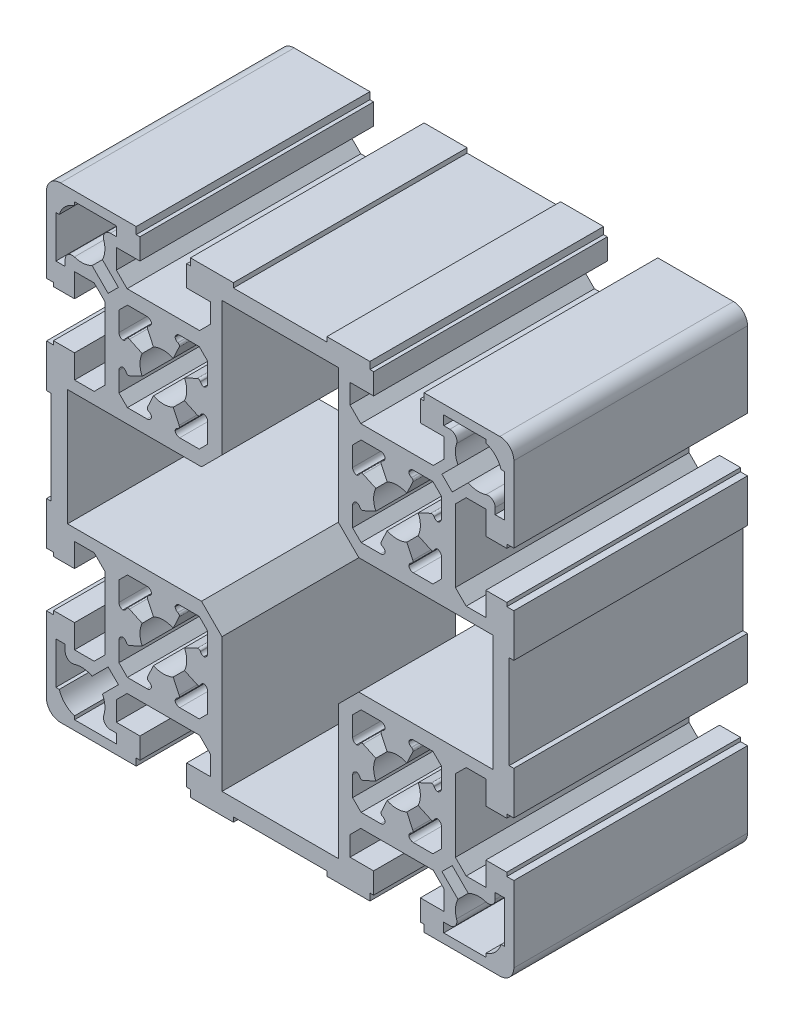
SolidWorks part; units mm, degrees
material "АД31Т ГОСТ 4784-97"
ref_plane "Front Plane" through (0, 0, 0) normal (0, 0, 1) x (1, 0, 0)
ref_plane "Top Plane" through (0, 0, 0) normal (0, 1, 0) x (1, 0, 0)
ref_plane "Right Plane" through (0, 0, 0) normal (1, 0, 0) x (0, 0, -1)
sketch "Sketch1" plane through (0, 0, 0) normal (0, 0, 1) x (1, 0, 0)
  line L0 (-15.5014, -32.6803) -> (-17.3205, -34.4994)
  line L1 (-12.45, -16.8336) -> (-16.8336, -12.45)
  line L2 (-17.25, -37.5) -> (-14.95, -39.8)
  line L3 (-14.95, -44) -> (-20, -44)
  line L4 (-19.2, -50) -> (-10, -50)
  line L5 (-35.05, -44) -> (-35.05, -39.8)
  line L6 (-50, -30.8) -> (-50, -47)
  line L7 (-48, -44) -> (-48, -35)
  line L8 (-47, -50) -> (-30.8, -50)
  line L9 (-35, -48) -> (-44, -48)
  line L10 (-44, -48) -> (-44, -47.2697)
  line L11 (-47.2697, -44) -> (-48, -44)
  line L12 (-20, -44) -> (-20, -48.5)
  line L13 (-30, -48.5) -> (-30, -44)
  line L14 (-35, -46) -> (-35, -48)
  line L15 (-30.8, -50) -> (-30.8, -48.5)
  line L16 (-30.8, -48.5) -> (-30, -48.5)
  line L17 (-20, -48.5) -> (-19.2, -48.5)
  line L18 (-19.2, -48.5) -> (-19.2, -50)
  line L19 (-30, -44) -> (-35.05, -44)
  line L20 (-36.3153, -46) -> (-35, -46)
  line L21 (-22.8883, -20.4679) -> (-21.6205, -17.7489)
  line L22 (-28.3809, -17.7495) -> (-27.1136, -20.4674)
  line L23 (-34.5, -21.5) -> (-34.5, -17.3191)
  line L24 (-44, -20) -> (-44, -14.95)
  line L25 (-50, -10) -> (-50, -19.2)
  line L26 (-37.5, -17.25) -> (-37.5, -32.75)
  line L27 (-21.6205, -32.2499) -> (-22.8883, -29.531)
  line L28 (-27.1145, -29.531) -> (-28.3824, -32.2499)
  line L29 (-34.5014, -32.6803) -> (-34.5014, -28.4994)
  line L30 (-37.5, -32.75) -> (-39.8, -35.05)
  line L31 (-40.2429, -38.0385) -> (-36.814, -34.6096)
  line L32 (-34.6096, -36.814) -> (-38.0385, -40.2429)
  line L33 (-46, -35) -> (-46, -36.3153)
  line L34 (-44, -30) -> (-48.5, -30)
  line L35 (-48.5, -30) -> (-48.5, -30.8)
  line L36 (-48.5, -30.8) -> (-50, -30.8)
  line L37 (-39.8, -35.05) -> (-44, -35.05)
  line L38 (-44, -35.05) -> (-44, -30)
  line L39 (-48, -35) -> (-46, -35)
  line L40 (-36.814, -34.6096) -> (-34.6096, -36.814)
  line L41 (-32.75, -37.5) -> (-17.25, -37.5)
  line L42 (-35.05, -39.8) -> (-32.75, -37.5)
  line L43 (-28.1405, -32.9143) -> (-28.0788, -32.9431)
  line L44 (-28.5014, -34.4994) -> (-32.6823, -34.4994)
  line L45 (-32.6823, -34.4994) -> (-34.5014, -32.6803)
  line L46 (-17.3205, -34.4994) -> (-21.5014, -34.4994)
  line L47 (-21.924, -32.9431) -> (-21.8623, -32.9143)
  line L48 (-48.5, -20) -> (-44, -20)
  line L49 (-50, -19.2) -> (-48.5, -19.2)
  line L50 (-48.5, -19.2) -> (-48.5, -20)
  line L51 (-32.9451, -28.0768) -> (-32.9164, -28.1385)
  line L52 (-32.2519, -28.3804) -> (-29.533, -27.1125)
  line L53 (-20.4699, -27.1125) -> (-17.751, -28.3804)
  line L54 (-17.0865, -28.1385) -> (-17.0577, -28.0768)
  line L55 (-29.533, -22.8863) -> (-32.2519, -21.6185)
  line L56 (-32.9164, -21.8603) -> (-32.9437, -21.9226)
  line L57 (-17.0577, -21.922) -> (-17.0865, -21.8603)
  line L58 (-17.751, -21.6185) -> (-20.4699, -22.8863)
  line L59 (-39.8, -14.95) -> (-37.5, -17.25)
  line L60 (-16.8336, -12.45) -> (-45.5, -12.45)
  line L61 (-44, -14.95) -> (-39.8, -14.95)
  line L62 (-49, -10) -> (-50, -10)
  line L63 (-28.0774, -17.0563) -> (-28.1391, -17.0851)
  line L64 (-34.5, -17.3191) -> (-32.6809, -15.5)
  line L65 (-32.6809, -15.5) -> (-28.5, -15.5)
  line L66 (-21.8623, -17.0845) -> (-21.924, -17.0557)
  line L67 (-21.5014, -15.4994) -> (-17.3205, -15.4994)
  line L68 (50, -47) -> (50, -30.8)
  line L69 (48, -35) -> (48, -44)
  line L70 (35.05, -39.8) -> (35.05, -44)
  line L71 (14.95, -44) -> (14.95, -39.8)
  line L72 (12.45, -16.8336) -> (12.45, -45.5)
  line L73 (-14.95, -39.8) -> (-14.95, -44)
  line L74 (-12.45, -45.5) -> (-12.45, -16.8336)
  line L75 (12.45, -45.5) -> (-12.45, -45.5)
  line L76 (-10, -49) -> (10, -49)
  line L77 (-10, -50) -> (-10, -49)
  line L78 (20, -48.5) -> (20, -44)
  line L79 (10, -50) -> (19.2, -50)
  line L80 (10, -49) -> (10, -50)
  line L81 (19.2, -50) -> (19.2, -48.5)
  line L82 (19.2, -48.5) -> (20, -48.5)
  line L83 (20, -44) -> (14.95, -44)
  line L84 (30, -44) -> (30, -48.5)
  line L85 (35, -48) -> (35, -46)
  line L86 (30.8, -50) -> (47, -50)
  line L87 (44, -48) -> (35, -48)
  line L88 (30, -48.5) -> (30.8, -48.5)
  line L89 (30.8, -48.5) -> (30.8, -50)
  line L90 (44, -47.2697) -> (44, -48)
  line L91 (35.05, -44) -> (30, -44)
  line L92 (35, -46) -> (36.3153, -46)
  line L93 (48, -44) -> (47.2697, -44)
  line L94 (50, -19.2) -> (50, -10)
  line L95 (44, -14.95) -> (44, -20)
  line L96 (34.5, -17.3191) -> (34.5, -21.5)
  line L97 (37.5, -32.75) -> (37.5, -17.25)
  line L98 (21.6191, -17.7495) -> (22.8869, -20.4685)
  line L99 (27.1131, -20.4685) -> (28.3809, -17.7495)
  line L100 (15.5, -21.5) -> (15.5, -17.3191)
  line L101 (-15.5014, -17.3185) -> (-15.5014, -21.4994)
  line L102 (28.3809, -32.2505) -> (27.1131, -29.5315)
  line L103 (17.25, -37.5) -> (32.75, -37.5)
  line L104 (22.8869, -29.5315) -> (21.6191, -32.2505)
  line L105 (15.5, -32.6809) -> (15.5, -28.5)
  line L106 (-15.5014, -28.4994) -> (-15.5014, -32.6803)
  line L107 (14.95, -39.8) -> (17.25, -37.5)
  line L108 (17.3191, -34.5) -> (15.5, -32.6809)
  line L109 (21.8609, -32.9149) -> (21.9226, -32.9437)
  line L110 (21.5, -34.5) -> (17.3191, -34.5)
  line L111 (17.7495, -28.3809) -> (20.4685, -27.1131)
  line L112 (17.0563, -28.0774) -> (17.0851, -28.1391)
  line L113 (20.4685, -22.8869) -> (17.7495, -21.6191)
  line L114 (17.0851, -21.8609) -> (17.0563, -21.9226)
  line L115 (34.5, -28.5) -> (34.5, -32.6809)
  line L116 (50, -30.8) -> (48.5, -30.8)
  line L117 (46, -36.3153) -> (46, -35)
  line L118 (34.6096, -36.814) -> (36.814, -34.6096)
  line L119 (36.814, -34.6096) -> (40.2429, -38.0385)
  line L120 (32.75, -37.5) -> (35.05, -39.8)
  line L121 (38.0385, -40.2429) -> (34.6096, -36.814)
  line L122 (39.8, -35.05) -> (37.5, -32.75)
  line L123 (34.5, -32.6809) -> (32.6809, -34.5)
  line L124 (32.6809, -34.5) -> (28.5, -34.5)
  line L125 (28.0774, -32.9437) -> (28.1391, -32.9149)
  line L126 (48.5, -30.8) -> (48.5, -30)
  line L127 (44, -30) -> (44, -35.05)
  line L128 (44, -35.05) -> (39.8, -35.05)
  line L129 (48.5, -30) -> (44, -30)
  line L130 (46, -35) -> (48, -35)
  line L131 (48.5, -19.2) -> (50, -19.2)
  line L132 (29.5315, -27.1131) -> (32.2505, -28.3809)
  line L133 (32.9149, -28.1391) -> (32.9437, -28.0774)
  line L134 (32.9437, -21.9226) -> (32.9149, -21.8609)
  line L135 (32.2505, -21.6191) -> (29.5315, -22.8869)
  line L136 (48.5, -20) -> (48.5, -19.2)
  line L137 (44, -20) -> (48.5, -20)
  line L138 (45.5, -12.45) -> (16.8336, -12.45)
  line L139 (15.5, -17.3191) -> (17.3191, -15.5)
  line L140 (16.8336, -12.45) -> (12.45, -16.8336)
  line L141 (21.9226, -17.0563) -> (21.8609, -17.0851)
  line L142 (17.3191, -15.5) -> (21.5, -15.5)
  line L143 (50, -10) -> (49, -10)
  line L144 (37.5, -17.25) -> (39.8, -14.95)
  line L145 (28.5, -15.5) -> (32.6809, -15.5)
  line L146 (32.6809, -15.5) -> (34.5, -17.3191)
  line L147 (28.1391, -17.0851) -> (28.0774, -17.0563)
  line L148 (39.8, -14.95) -> (44, -14.95)
  line L149 (-17.3191, 34.5) -> (-15.5, 32.6809)
  line L150 (-15.5, 17.3191) -> (-17.3191, 15.5)
  line L151 (-16.8336, 12.45) -> (-12.45, 16.8336)
  line L152 (-10, 50) -> (-19.2, 50)
  line L153 (-20, 44) -> (-14.95, 44)
  line L154 (-14.95, 39.8) -> (-17.25, 37.5)
  line L155 (-37.5, 32.75) -> (-37.5, 17.25)
  line L156 (-32.6809, 15.5) -> (-34.5, 17.3191)
  line L157 (-37.5, 17.25) -> (-39.8, 14.95)
  line L158 (-44, 14.95) -> (-44, 20)
  line L159 (-50, 19.2) -> (-50, 10)
  line L160 (-45.5, 12.45) -> (-16.8336, 12.45)
  line L161 (-50, 10) -> (-49, 10)
  line L162 (-39.8, 14.95) -> (-44, 14.95)
  line L163 (-28.5, 15.5) -> (-32.6809, 15.5)
  line L164 (-17.3191, 15.5) -> (-21.5, 15.5)
  line L165 (-44, 20) -> (-48.5, 20)
  line L166 (-48.5, 20) -> (-48.5, 19.2)
  line L167 (-48.5, 19.2) -> (-50, 19.2)
  line L168 (-20.4685, 22.8869) -> (-17.7495, 21.6191)
  line L169 (-32.2505, 21.6191) -> (-29.5315, 22.8869)
  line L170 (-34.5, 17.3191) -> (-34.5, 21.5)
  line L171 (-32.9437, 21.9226) -> (-32.9149, 21.8609)
  line L172 (-27.1131, 20.4685) -> (-28.3809, 17.7495)
  line L173 (-28.1391, 17.0851) -> (-28.0774, 17.0563)
  line L174 (-17.0851, 21.8609) -> (-17.0563, 21.9226)
  line L175 (-21.9226, 17.0563) -> (-21.8609, 17.0851)
  line L176 (-21.6191, 17.7495) -> (-22.8869, 20.4685)
  line L177 (-29.5315, 27.1131) -> (-32.2505, 28.3809)
  line L178 (-32.9149, 28.1391) -> (-32.9437, 28.0774)
  line L179 (-17.0563, 28.0774) -> (-17.0851, 28.1391)
  line L180 (-17.7495, 28.3809) -> (-20.4685, 27.1131)
  line L181 (-35.05, 39.8) -> (-35.05, 44)
  line L182 (-50, 47) -> (-50, 30.8)
  line L183 (-48, 35) -> (-48, 44)
  line L184 (-38.0385, 40.2429) -> (-34.6096, 36.814)
  line L185 (-39.8, 35.05) -> (-37.5, 32.75)
  line L186 (-36.814, 34.6096) -> (-40.2429, 38.0385)
  line L187 (-44, 30) -> (-44, 35.05)
  line L188 (-48.5, 30) -> (-44, 30)
  line L189 (-50, 30.8) -> (-48.5, 30.8)
  line L190 (-48.5, 30.8) -> (-48.5, 30)
  line L191 (-44, 35.05) -> (-39.8, 35.05)
  line L192 (-46, 36.3153) -> (-46, 35)
  line L193 (-46, 35) -> (-48, 35)
  line L194 (-34.5, 32.6809) -> (-32.6809, 34.5)
  line L195 (-34.5, 28.5) -> (-34.5, 32.6809)
  line L196 (-28.0774, 32.9437) -> (-28.1397, 32.9164)
  line L197 (-28.3815, 32.2519) -> (-27.113, 29.5316)
  line L198 (-22.8869, 29.5315) -> (-21.6191, 32.2505)
  line L199 (-21.8609, 32.9149) -> (-21.9226, 32.9437)
  line L200 (-17.25, 37.5) -> (-32.75, 37.5)
  line L201 (-32.75, 37.5) -> (-35.05, 39.8)
  line L202 (-32.6809, 34.5) -> (-28.5, 34.5)
  line L203 (-34.6096, 36.814) -> (-36.814, 34.6096)
  line L204 (-21.5, 34.5) -> (-17.3191, 34.5)
  line L205 (-30.8, 50) -> (-47, 50)
  line L206 (-44, 48) -> (-35, 48)
  line L207 (-48, 44) -> (-47.2697, 44)
  line L208 (-44, 47.2697) -> (-44, 48)
  line L209 (-20, 48.5) -> (-20, 44)
  line L210 (-30, 44) -> (-30, 48.5)
  line L211 (-35.05, 44) -> (-30, 44)
  line L212 (-30, 48.5) -> (-30.8, 48.5)
  line L213 (-30.8, 48.5) -> (-30.8, 50)
  line L214 (-35, 48) -> (-35, 46)
  line L215 (-35, 46) -> (-36.3153, 46)
  line L216 (-19.2, 50) -> (-19.2, 48.5)
  line L217 (-19.2, 48.5) -> (-20, 48.5)
  line L218 (37.5, 17.25) -> (37.5, 32.75)
  line L219 (12.45, 45.5) -> (12.45, 16.8336)
  line L220 (-12.45, 16.8336) -> (-12.45, 45.5)
  line L221 (28.3809, 17.7495) -> (27.1131, 20.4685)
  line L222 (16.8336, 12.45) -> (45.5, 12.45)
  line L223 (17.3191, 15.5) -> (15.5, 17.3191)
  line L224 (12.45, 16.8336) -> (16.8336, 12.45)
  line L225 (21.5, 15.5) -> (17.3191, 15.5)
  line L226 (-15.5, 21.5) -> (-15.5, 17.3191)
  line L227 (17.7495, 21.6191) -> (20.4685, 22.8869)
  line L228 (15.5, 17.3191) -> (15.5, 21.5)
  line L229 (22.8869, 20.4685) -> (21.6191, 17.7495)
  line L230 (21.8609, 17.0851) -> (21.9226, 17.0563)
  line L231 (17.0563, 21.9226) -> (17.0851, 21.8609)
  line L232 (20.4685, 27.1131) -> (17.7495, 28.3809)
  line L233 (17.0851, 28.1391) -> (17.0563, 28.0774)
  line L234 (44, 20) -> (44, 14.95)
  line L235 (34.5, 17.3191) -> (32.6809, 15.5)
  line L236 (39.8, 14.95) -> (37.5, 17.25)
  line L237 (50, 10) -> (50, 19.2)
  line L238 (49, 10) -> (50, 10)
  line L239 (32.6809, 15.5) -> (28.5, 15.5)
  line L240 (44, 14.95) -> (39.8, 14.95)
  line L241 (50, 19.2) -> (48.5, 19.2)
  line L242 (29.5315, 22.8869) -> (32.2505, 21.6191)
  line L243 (32.9149, 21.8609) -> (32.9437, 21.9226)
  line L244 (34.5, 21.5) -> (34.5, 17.3191)
  line L245 (28.0774, 17.0563) -> (28.1391, 17.0851)
  line L246 (48.5, 19.2) -> (48.5, 20)
  line L247 (48.5, 20) -> (44, 20)
  line L248 (32.9431, 28.076) -> (32.9143, 28.1377)
  line L249 (32.2499, 28.3795) -> (29.532, 27.1121)
  line L250 (27.1131, 29.5315) -> (28.3809, 32.2505)
  line L251 (32.75, 37.5) -> (17.25, 37.5)
  line L252 (14.95, 39.8) -> (14.95, 44)
  line L253 (-14.95, 44) -> (-14.95, 39.8)
  line L254 (-15.5, 32.6809) -> (-15.5, 28.5)
  line L255 (15.5, 32.6809) -> (17.3191, 34.5)
  line L256 (15.5, 28.5) -> (15.5, 32.6809)
  line L257 (21.9226, 32.9437) -> (21.8603, 32.9164)
  line L258 (21.6185, 32.2519) -> (22.887, 29.5316)
  line L259 (17.25, 37.5) -> (14.95, 39.8)
  line L260 (17.3191, 34.5) -> (21.5, 34.5)
  line L261 (-12.45, 45.5) -> (12.45, 45.5)
  line L262 (10, 49) -> (-10, 49)
  line L263 (-10, 49) -> (-10, 50)
  line L264 (20, 44) -> (20, 48.5)
  line L265 (14.95, 44) -> (20, 44)
  line L266 (19.2, 50) -> (10, 50)
  line L267 (10, 50) -> (10, 49)
  line L268 (20, 48.5) -> (19.2, 48.5)
  line L269 (19.2, 48.5) -> (19.2, 50)
  line L270 (50, 30.8) -> (50, 47)
  line L271 (48, 44) -> (48, 35)
  line L272 (35.05, 44) -> (35.05, 39.8)
  line L273 (34.6096, 36.814) -> (38.0385, 40.2429)
  line L274 (48.5, 30.8) -> (50, 30.8)
  line L275 (44, 35.05) -> (44, 30)
  line L276 (32.6803, 34.4986) -> (34.4994, 32.6795)
  line L277 (37.5, 32.75) -> (39.8, 35.05)
  line L278 (34.4994, 32.6795) -> (34.4994, 28.4986)
  line L279 (28.1391, 32.9149) -> (28.0768, 32.9423)
  line L280 (48.5, 30) -> (48.5, 30.8)
  line L281 (44, 30) -> (48.5, 30)
  line L282 (40.2429, 38.0385) -> (36.814, 34.6096)
  line L283 (35.05, 39.8) -> (32.75, 37.5)
  line L284 (28.4994, 34.4986) -> (32.6803, 34.4986)
  line L285 (36.814, 34.6096) -> (34.6096, 36.814)
  line L286 (39.8, 35.05) -> (44, 35.05)
  line L287 (46, 35) -> (46, 36.3153)
  line L288 (48, 35) -> (46, 35)
  line L289 (30, 48.5) -> (30, 44)
  line L290 (30, 44) -> (35.05, 44)
  line L291 (47.2697, 44) -> (48, 44)
  line L292 (47, 50) -> (30.8, 50)
  line L293 (35, 48) -> (44, 48)
  line L294 (30.8, 50) -> (30.8, 48.5)
  line L295 (30.8, 48.5) -> (30, 48.5)
  line L296 (36.3153, 46) -> (35, 46)
  line L297 (35, 46) -> (35, 48)
  line L298 (44, 48) -> (44, 47.2697)
  line L299 (-49, 10) -> (-49, -10)
  line L300 (-45.5, 12.45) -> (-45.5, -12.45)
  line L301 (45.5, 12.45) -> (45.5, -12.45)
  line L302 (49, 10) -> (49, -10)
  line L303 (0, 53.1587) -> (0, -54.0147) construction
  line L304 (-52.9019, 0) -> (53.2443, 0) construction
  line L305 (-17.3205, -15.4994) -> (-15.5014, -17.3185)
  arc A0 (-16.3264, -22.484) -> (-15.5014, -21.4994) centre (-16.5014, -21.4994) ccw
  arc A1 (-15.5014, -28.4994) -> (-16.3264, -27.5148) centre (-16.5014, -28.4994) ccw
  arc A2 (-37.7426, -44.0385) -> (-38.0385, -40.2429) centre (-42.5, -42.5) ccw
  arc A3 (-37.7426, -44.0385) -> (-36.3153, -46) centre (-36.3153, -44.5) ccw
  arc A4 (-47.2697, -44) -> (-44, -47.2697) centre (-42.5, -42.5) ccw
  arc A5 (-50, -47) -> (-47, -50) centre (-47, -47) ccw
  arc A6 (-27.1145, -29.531) -> (-22.8883, -29.531) centre (-25.0014, -24.9994) ccw
  arc A7 (-46, -36.3153) -> (-44.0385, -37.7426) centre (-44.5, -36.3153) ccw
  arc A8 (-40.2429, -38.0385) -> (-44.0385, -37.7426) centre (-42.5, -42.5) ccw
  arc A9 (-28.3824, -32.2499) -> (-28.1405, -32.9143) centre (-27.9292, -32.4612) ccw
  arc A10 (-27.5169, -33.6744) -> (-28.0788, -32.9431) centre (-28.5014, -33.8494) ccw
  arc A11 (-28.5014, -34.4994) -> (-27.5169, -33.6744) centre (-28.5014, -33.4994) ccw
  arc A12 (-22.486, -33.6744) -> (-21.5014, -34.4994) centre (-21.5014, -33.4994) ccw
  arc A13 (-21.924, -32.9431) -> (-22.486, -33.6744) centre (-21.5014, -33.8494) ccw
  arc A14 (-21.8623, -32.9143) -> (-21.6205, -32.2499) centre (-22.0736, -32.4612) ccw
  arc A15 (-20.4699, -27.1125) -> (-20.4699, -22.8863) centre (-25.0014, -24.9994) ccw
  arc A16 (-29.533, -22.8863) -> (-29.533, -27.1125) centre (-25.0014, -24.9994) ccw
  arc A17 (-33.6764, -27.5148) -> (-34.5014, -28.4994) centre (-33.5014, -28.4994) ccw
  arc A18 (-32.9451, -28.0768) -> (-33.6764, -27.5148) centre (-33.8514, -28.4994) ccw
  arc A19 (-32.9164, -28.1385) -> (-32.2519, -28.3804) centre (-32.4632, -27.9272) ccw
  arc A20 (-17.751, -28.3804) -> (-17.0865, -28.1385) centre (-17.5397, -27.9272) ccw
  arc A21 (-16.3264, -27.5148) -> (-17.0577, -28.0768) centre (-16.1514, -28.4994) ccw
  arc A22 (-22.8883, -20.4679) -> (-27.1136, -20.4674) centre (-25.0014, -24.9994) ccw
  arc A23 (-32.2519, -21.6185) -> (-32.9164, -21.8603) centre (-32.4632, -22.0716) ccw
  arc A24 (-33.675, -22.4846) -> (-32.9437, -21.9226) centre (-33.85, -21.5) ccw
  arc A25 (-34.5, -21.5) -> (-33.675, -22.4846) centre (-33.5, -21.5) ccw
  arc A26 (-17.0577, -21.922) -> (-16.3264, -22.484) centre (-16.1514, -21.4994) ccw
  arc A27 (-17.0865, -21.8603) -> (-17.751, -21.6185) centre (-17.5397, -22.0716) ccw
  arc A28 (-28.0774, -17.0563) -> (-27.5154, -16.325) centre (-28.5, -16.15) ccw
  arc A29 (-28.1391, -17.0851) -> (-28.3809, -17.7495) centre (-27.9278, -17.5382) ccw
  arc A30 (-27.5154, -16.325) -> (-28.5, -15.5) centre (-28.5, -16.5) ccw
  arc A31 (-21.6205, -17.7489) -> (-21.8623, -17.0845) centre (-22.0736, -17.5376) ccw
  arc A32 (-22.486, -16.3244) -> (-21.924, -17.0557) centre (-21.5014, -16.1494) ccw
  arc A33 (-21.5014, -15.4994) -> (-22.486, -16.3244) centre (-21.5014, -16.4994) ccw
  arc A34 (38.0385, -40.2429) -> (37.7426, -44.0385) centre (42.5, -42.5) ccw
  arc A35 (47, -50) -> (50, -47) centre (47, -47) ccw
  arc A36 (44, -47.2697) -> (47.2697, -44) centre (42.5, -42.5) ccw
  arc A37 (36.3153, -46) -> (37.7426, -44.0385) centre (36.3153, -44.5) ccw
  arc A38 (28.0774, -32.9437) -> (27.5154, -33.675) centre (28.5, -33.85) ccw
  arc A39 (27.5154, -33.675) -> (28.5, -34.5) centre (28.5, -33.5) ccw
  arc A40 (22.8869, -29.5315) -> (27.1131, -29.5315) centre (25, -25) ccw
  arc A41 (21.6191, -32.2505) -> (21.8609, -32.9149) centre (22.0722, -32.4618) ccw
  arc A42 (22.4846, -33.675) -> (21.9226, -32.9437) centre (21.5, -33.85) ccw
  arc A43 (21.5, -34.5) -> (22.4846, -33.675) centre (21.5, -33.5) ccw
  arc A44 (20.4685, -22.8869) -> (20.4685, -27.1131) centre (25, -25) ccw
  arc A45 (17.0563, -28.0774) -> (16.325, -27.5154) centre (16.15, -28.5) ccw
  arc A46 (16.325, -27.5154) -> (15.5, -28.5) centre (16.5, -28.5) ccw
  arc A47 (17.0851, -28.1391) -> (17.7495, -28.3809) centre (17.5382, -27.9278) ccw
  arc A48 (16.325, -22.4846) -> (17.0563, -21.9226) centre (16.15, -21.5) ccw
  arc A49 (15.5, -21.5) -> (16.325, -22.4846) centre (16.5, -21.5) ccw
  arc A50 (27.1131, -20.4685) -> (22.8869, -20.4685) centre (25, -25) ccw
  arc A51 (17.7495, -21.6191) -> (17.0851, -21.8609) centre (17.5382, -22.0722) ccw
  arc A52 (44.0385, -37.7426) -> (40.2429, -38.0385) centre (42.5, -42.5) ccw
  arc A53 (44.0385, -37.7426) -> (46, -36.3153) centre (44.5, -36.3153) ccw
  arc A54 (28.1391, -32.9149) -> (28.3809, -32.2505) centre (27.9278, -32.4618) ccw
  arc A55 (29.5315, -27.1131) -> (29.5315, -22.8869) centre (25, -25) ccw
  arc A56 (32.2505, -28.3809) -> (32.9149, -28.1391) centre (32.4618, -27.9278) ccw
  arc A57 (33.675, -27.5154) -> (32.9437, -28.0774) centre (33.85, -28.5) ccw
  arc A58 (34.5, -28.5) -> (33.675, -27.5154) centre (33.5, -28.5) ccw
  arc A59 (33.675, -22.4846) -> (34.5, -21.5) centre (33.5, -21.5) ccw
  arc A60 (32.9437, -21.9226) -> (33.675, -22.4846) centre (33.85, -21.5) ccw
  arc A61 (32.9149, -21.8609) -> (32.2505, -21.6191) centre (32.4618, -22.0722) ccw
  arc A62 (27.5154, -16.325) -> (28.0774, -17.0563) centre (28.5, -16.15) ccw
  arc A63 (28.5, -15.5) -> (27.5154, -16.325) centre (28.5, -16.5) ccw
  arc A64 (22.4846, -16.325) -> (21.5, -15.5) centre (21.5, -16.5) ccw
  arc A65 (21.9226, -17.0563) -> (22.4846, -16.325) centre (21.5, -16.15) ccw
  arc A66 (21.8609, -17.0851) -> (21.6191, -17.7495) centre (22.0722, -17.5382) ccw
  arc A67 (28.3809, -17.7495) -> (28.1391, -17.0851) centre (27.9278, -17.5382) ccw
  arc A68 (-16.325, 27.5154) -> (-15.5, 28.5) centre (-16.5, 28.5) ccw
  arc A69 (-15.5, 21.5) -> (-16.325, 22.4846) centre (-16.5, 21.5) ccw
  arc A70 (-17.0851, 28.1391) -> (-17.7495, 28.3809) centre (-17.5382, 27.9278) ccw
  arc A71 (-32.2505, 28.3809) -> (-32.9149, 28.1391) centre (-32.4618, 27.9278) ccw
  arc A72 (-34.5, 28.5) -> (-33.675, 27.5154) centre (-33.5, 28.5) ccw
  arc A73 (-21.9226, 17.0563) -> (-22.4846, 16.325) centre (-21.5, 16.15) ccw
  arc A74 (-27.5154, 16.325) -> (-28.0774, 17.0563) centre (-28.5, 16.15) ccw
  arc A75 (-28.5, 15.5) -> (-27.5154, 16.325) centre (-28.5, 16.5) ccw
  arc A76 (-22.4846, 16.325) -> (-21.5, 15.5) centre (-21.5, 16.5) ccw
  arc A77 (-33.675, 22.4846) -> (-34.5, 21.5) centre (-33.5, 21.5) ccw
  arc A78 (-27.1131, 20.4685) -> (-22.8869, 20.4685) centre (-25, 25) ccw
  arc A79 (-32.9437, 21.9226) -> (-33.675, 22.4846) centre (-33.85, 21.5) ccw
  arc A80 (-32.9149, 21.8609) -> (-32.2505, 21.6191) centre (-32.4618, 22.0722) ccw
  arc A81 (-28.3809, 17.7495) -> (-28.1391, 17.0851) centre (-27.9278, 17.5382) ccw
  arc A82 (-17.7495, 21.6191) -> (-17.0851, 21.8609) centre (-17.5382, 22.0722) ccw
  arc A83 (-16.325, 22.4846) -> (-17.0563, 21.9226) centre (-16.15, 21.5) ccw
  arc A84 (-21.8609, 17.0851) -> (-21.6191, 17.7495) centre (-22.0722, 17.5382) ccw
  arc A85 (-29.5315, 27.1131) -> (-29.5315, 22.8869) centre (-25, 25) ccw
  arc A86 (-33.675, 27.5154) -> (-32.9437, 28.0774) centre (-33.85, 28.5) ccw
  arc A87 (-17.0563, 28.0774) -> (-16.325, 27.5154) centre (-16.15, 28.5) ccw
  arc A88 (-20.4685, 22.8869) -> (-20.4685, 27.1131) centre (-25, 25) ccw
  arc A89 (-44.0385, 37.7426) -> (-40.2429, 38.0385) centre (-42.5, 42.5) ccw
  arc A90 (-44.0385, 37.7426) -> (-46, 36.3153) centre (-44.5, 36.3153) ccw
  arc A91 (-21.5, 34.5) -> (-22.4846, 33.675) centre (-21.5, 33.5) ccw
  arc A92 (-27.5154, 33.675) -> (-28.5, 34.5) centre (-28.5, 33.5) ccw
  arc A93 (-22.8869, 29.5315) -> (-27.113, 29.5316) centre (-25, 25) ccw
  arc A94 (-28.0774, 32.9437) -> (-27.5154, 33.675) centre (-28.5, 33.85) ccw
  arc A95 (-28.1397, 32.9164) -> (-28.3815, 32.2519) centre (-27.9284, 32.4632) ccw
  arc A96 (-21.6191, 32.2505) -> (-21.8609, 32.9149) centre (-22.0722, 32.4618) ccw
  arc A97 (-22.4846, 33.675) -> (-21.9226, 32.9437) centre (-21.5, 33.85) ccw
  arc A98 (-38.0385, 40.2429) -> (-37.7426, 44.0385) centre (-42.5, 42.5) ccw
  arc A99 (-36.3153, 46) -> (-37.7426, 44.0385) centre (-36.3153, 44.5) ccw
  arc A100 (-44, 47.2697) -> (-47.2697, 44) centre (-42.5, 42.5) ccw
  arc A101 (-47, 50) -> (-50, 47) centre (-47, 47) ccw
  arc A102 (33.6744, 27.514) -> (34.4994, 28.4986) centre (33.4994, 28.4986) ccw
  arc A103 (32.9143, 28.1377) -> (32.2499, 28.3795) centre (32.4612, 27.9264) ccw
  arc A104 (15.5, 28.5) -> (16.325, 27.5154) centre (16.5, 28.5) ccw
  arc A105 (17.7495, 28.3809) -> (17.0851, 28.1391) centre (17.5382, 27.9278) ccw
  arc A106 (28.0774, 17.0563) -> (27.5154, 16.325) centre (28.5, 16.15) ccw
  arc A107 (27.5154, 16.325) -> (28.5, 15.5) centre (28.5, 16.5) ccw
  arc A108 (22.4846, 16.325) -> (21.9226, 17.0563) centre (21.5, 16.15) ccw
  arc A109 (21.5, 15.5) -> (22.4846, 16.325) centre (21.5, 16.5) ccw
  arc A110 (16.325, 22.4846) -> (15.5, 21.5) centre (16.5, 21.5) ccw
  arc A111 (17.0563, 21.9226) -> (16.325, 22.4846) centre (16.15, 21.5) ccw
  arc A112 (22.8869, 20.4685) -> (27.1131, 20.4685) centre (25, 25) ccw
  arc A113 (21.6191, 17.7495) -> (21.8609, 17.0851) centre (22.0722, 17.5382) ccw
  arc A114 (17.0851, 21.8609) -> (17.7495, 21.6191) centre (17.5382, 22.0722) ccw
  arc A115 (16.325, 27.5154) -> (17.0563, 28.0774) centre (16.15, 28.5) ccw
  arc A116 (20.4685, 27.1131) -> (20.4685, 22.8869) centre (25, 25) ccw
  arc A117 (34.5, 21.5) -> (33.675, 22.4846) centre (33.5, 21.5) ccw
  arc A118 (32.2505, 21.6191) -> (32.9149, 21.8609) centre (32.4618, 22.0722) ccw
  arc A119 (33.675, 22.4846) -> (32.9437, 21.9226) centre (33.85, 21.5) ccw
  arc A120 (28.1391, 17.0851) -> (28.3809, 17.7495) centre (27.9278, 17.5382) ccw
  arc A121 (32.9431, 28.076) -> (33.6744, 27.514) centre (33.8494, 28.4986) ccw
  arc A122 (29.5315, 22.8869) -> (29.532, 27.1121) centre (25, 25) ccw
  arc A123 (27.5148, 33.6736) -> (28.0768, 32.9423) centre (28.4994, 33.8486) ccw
  arc A124 (28.4994, 34.4986) -> (27.5148, 33.6736) centre (28.4994, 33.4986) ccw
  arc A125 (22.4846, 33.675) -> (21.5, 34.5) centre (21.5, 33.5) ccw
  arc A126 (21.9226, 32.9437) -> (22.4846, 33.675) centre (21.5, 33.85) ccw
  arc A127 (21.8603, 32.9164) -> (21.6185, 32.2519) centre (22.0716, 32.4632) ccw
  arc A128 (27.1131, 29.5315) -> (22.887, 29.5316) centre (25, 25) ccw
  arc A129 (28.3809, 32.2505) -> (28.1391, 32.9149) centre (27.9278, 32.4618) ccw
  arc A130 (46, 36.3153) -> (44.0385, 37.7426) centre (44.5, 36.3153) ccw
  arc A131 (40.2429, 38.0385) -> (44.0385, 37.7426) centre (42.5, 42.5) ccw
  arc A132 (50, 47) -> (47, 50) centre (47, 47) ccw
  arc A133 (47.2697, 44) -> (44, 47.2697) centre (42.5, 42.5) ccw
  arc A134 (37.7426, 44.0385) -> (36.3153, 46) centre (36.3153, 44.5) ccw
  arc A135 (37.7426, 44.0385) -> (38.0385, 40.2429) centre (42.5, 42.5) ccw
  dimension "D3" = 10
  dimension "D4" = 10
  dimension "D6" = 10
  dimension "D1" = 100
  dimension "D2" = 100
extrude "Base-Extrude" add sketch "Sketch1" against normal blind 50
